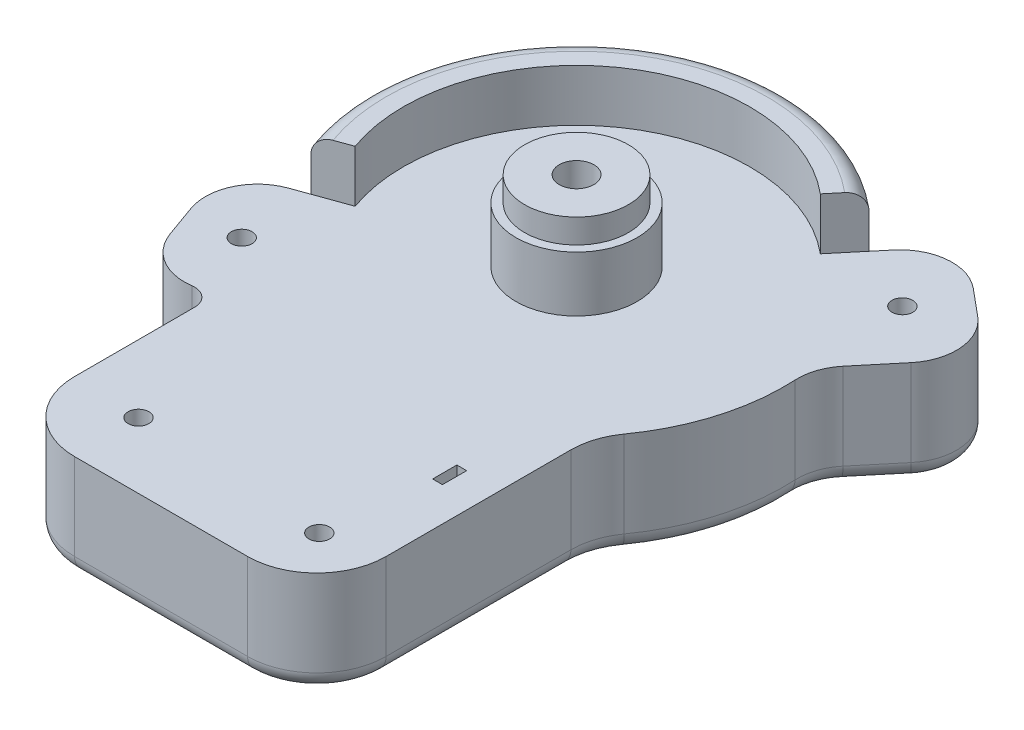
SolidWorks part; units mm, degrees
ref_plane "Front Plane" through (0, 0, 0) normal (0, 0, 1) x (1, 0, 0)
ref_plane "Top Plane" through (0, 0, 0) normal (0, 1, 0) x (1, 0, 0)
ref_plane "Right Plane" through (0, 0, 0) normal (1, 0, 0) x (0, 0, -1)
sketch "Sketch1" plane through (0, 0, 0) normal (0, -1, 0) x (-1, 0, 0)
  line L8 (-155.9788, -669.5716) -> (-160.6854, -671.2593)
  line L9 (-166.367, -699.855) -> (-169.7423, -690.4419)
  line L10 (-144.4999, -714.6026) -> (-144.4999, -749.3201)
  line L11 (-124.4999, -769.3201) -> (-74.4999, -769.3201)
  line L12 (-54.4999, -695.957) -> (-54.4999, -749.3201)
  line L13 (-57.8879, -599.3857) -> (-61.0888, -603.2268)
  line L14 (-36.7618, -597.4652) -> (-29.0796, -603.867)
  line L15 (-36.1279, -635.7557) -> (-27.159, -624.9931)
  arc A10 (-36.1279, -635.7557) -> (-39.5836, -646.1508) centre (-24.6046, -645.3585) ccw
  arc A11 (-160.6854, -671.2593) -> (-169.7423, -690.4419) centre (-155.6225, -685.379) ccw
  arc A12 (-166.367, -699.855) -> (-150.1867, -709.65) centre (-152.2473, -694.7922) ccw
  arc A13 (-144.4999, -714.6026) -> (-150.1867, -709.65) centre (-149.4999, -714.6026) ccw
  arc A14 (-144.4999, -749.3201) -> (-124.4999, -769.3201) centre (-124.4999, -749.3201) ccw
  arc A15 (-74.4999, -769.3201) -> (-54.4999, -749.3201) centre (-74.4999, -749.3201) ccw
  arc A16 (-50.7499, -684.2978) -> (-54.4999, -695.957) centre (-34.4999, -695.957) ccw
  arc A17 (-50.7499, -684.2978) -> (-39.5836, -646.1508) centre (-99.4999, -649.3201) ccw
  arc A18 (-36.7618, -597.4652) -> (-57.8879, -599.3857) centre (-46.3646, -608.9885) ccw
  arc A19 (-27.159, -624.9931) -> (-29.0796, -603.867) centre (-38.6823, -615.3903) ccw
  arc A20 (-155.9788, -669.5716) -> (-61.0888, -603.2268) centre (-99.4999, -649.3201) cw
extrude "Boss-Extrude1" add sketch "Sketch1" along normal blind 30
sketch "Sketch3" plane through (0, -30, 0) normal (0, -1, 0) x (1, 0, 0)
  circle A0 centre (42.5234, 612.1894) radius 6
  circle A1 centre (155.0926, 690.4309) radius 6
  circle A2 centre (124.9764, 750.3578) radius 6
  circle A3 centre (70.026, 753.0951) radius 6
extrude "Cut-Extrude2" cut sketch "Sketch3" against normal blind 10
sketch "Sketch4" plane through (0, -20, 0) normal (0, -1, 0) x (1, 0, 0)
  circle A0 centre (42.5234, 612.1894) radius 3
  circle A1 centre (155.0926, 690.4309) radius 3
  circle A2 centre (124.9764, 750.3578) radius 3
  circle A3 centre (70.026, 753.0951) radius 3
extrude "Cut-Extrude3" cut sketch "Sketch4" against normal up to next
sketch "Sketch5" plane through (0, 0, 0) normal (0, 1, 0) x (1, 0, 0)
  circle A0 centre (99.4999, -649.3201) radius 17.5
extrude "Boss-Extrude2" add sketch "Sketch5" along normal blind 16
sketch "Sketch6" plane through (0, 16, 0) normal (0, 1, 0) x (1, 0, 0)
  circle A0 centre (99.4999, -649.3201) radius 15
extrude "Boss-Extrude3" add sketch "Sketch6" along normal blind 7
sketch "Sketch7" plane through (0, 0, 0) normal (0, 1, 0) x (1, 0, 0)
  line L0 (155.9788, -669.5716) -> (146.5656, -666.1964)
  line L1 (67.4906, -610.909) -> (61.0888, -603.2268)
  arc A0 (155.9788, -669.5716) -> (61.0888, -603.2268) centre (99.4999, -649.3201) ccw
  arc A1 (146.5656, -666.1964) -> (67.4906, -610.909) centre (99.4998, -649.3201) ccw
extrude "Boss-Extrude4" add sketch "Sketch7" along normal blind 15
fillet "Fillet1" radius 5 20 edges at (158.3321, -30, 670.4154) (169.1867, -30, 678.9748) (168.0547, -30, 695.1485) (160.0152, -30, 707.6241) (146.2161, -30, 710.832) (144.4999, -30, 731.9613) (138.642, -30, 763.4622) (99.4999, -30, 769.3201) (60.3577, -30, 763.4622) (59.4883, -30, 601.3063) (47.7226, -30, 594.0501) (32.9207, -30, 600.6661) (23.7439, -30, 614.0323) (31.6435, -30, 630.3744) (38.8386, -30, 640.6265) (41.9161, -30, 666.1758) (53.5393, -30, 689.8333) (133.8804, -30, 600.1471) (54.4999, -30, 722.6385) (133.8804, 15, 600.1471)
mirror "Mirror1" about plane through (0, 0, 0) normal (1, 0, 0) of bodies 107
delete or keep bodies "Body-Delete/Keep 1" type delete bodies bodies 107
sketch "Sketch8" plane through (0, 23, 0) normal (0, 1, 0) x (1, 0, 0)
  circle A0 centre (-99.4999, -649.3201) radius 5
extrude "Cut-Extrude4" cut sketch "Sketch8" against normal up to next
sketch "Sketch9" plane through (0, 0, 0) normal (0, 1, 0) x (1, 0, 0)
  line L1 (-64.3305, -716.2201) -> (-67.1685, -716.2201)
  line L2 (-64.3305, -716.2201) -> (-64.3305, -723.2201)
  line L3 (-64.3305, -723.2201) -> (-67.1685, -723.2201)
  line L4 (-67.1685, -716.2201) -> (-67.1685, -723.2201)
extrude "Cut-Extrude5" cut sketch "Sketch9" against normal up to next
sketch "Sketch10" plane through (0, -30, 0) normal (0, -1, 0) x (1, 0, 0)
  line L0 (-67.1685, 716.2201) -> (-87.1686, 716.2201)
  line L1 (-67.1685, 716.2201) -> (-67.1685, 723.2201)
  line L2 (-67.1685, 723.2201) -> (-87.1686, 723.2201)
  line L3 (-95.5499, 649.3201) -> (-103.4499, 649.3201)
  line L4 (-95.5499, 649.3201) -> (-95.5499, 709.3196)
  line L5 (-103.4499, 649.3201) -> (-103.4499, 709.3201)
  arc A0 (-87.1686, 716.2201) -> (-95.5499, 709.3196) centre (-87.9092, 708.5795) ccw
  arc A1 (-87.1686, 723.2201) -> (-103.4499, 709.3201) centre (-88.3592, 708.1294) ccw
  point P10 (-99.4999, 649.3201)
extrude "Cut-Extrude6" cut sketch "Sketch10" against normal blind 10
